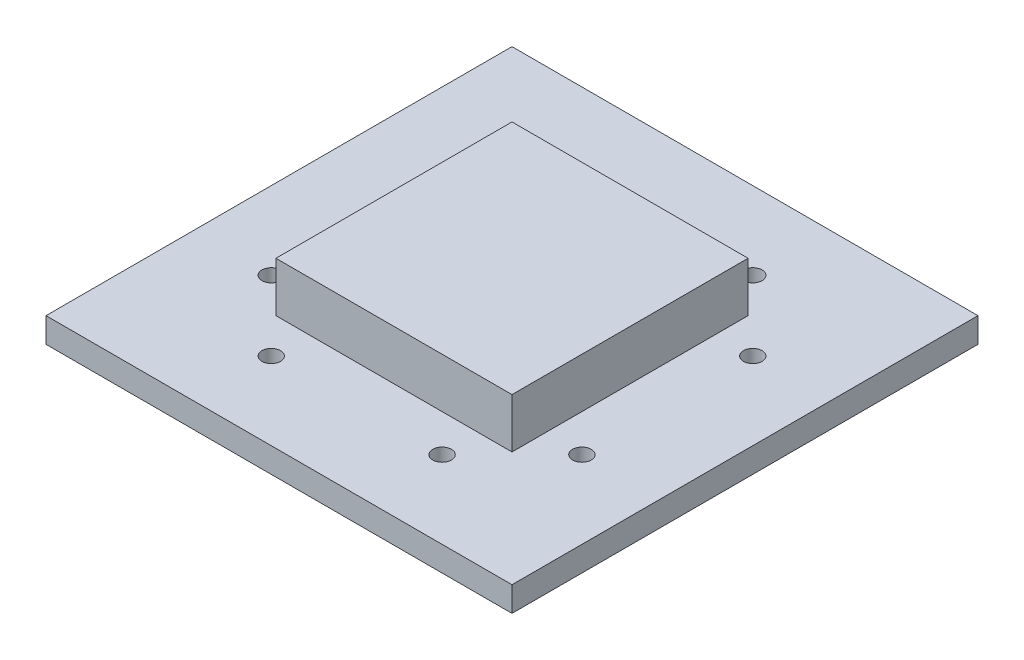
SolidWorks part; units mm, degrees
ref_plane "Front Plane" through (0, 0, 0) normal (0, 0, 1) x (1, 0, 0)
ref_plane "Top Plane" through (0, 0, 0) normal (0, 1, 0) x (1, 0, 0)
ref_plane "Right Plane" through (0, 0, 0) normal (1, 0, 0) x (0, 0, -1)
sketch "Sketch1" plane through (0, 0, 0) normal (0, 1, 0) x (1, 0, 0)
  line L0 (15, 0) -> (15, 30) construction
  line L1 (0, 0) -> (30, 0)
  line L2 (0, 0) -> (0, 30)
  line L3 (0, 30) -> (30, 30)
  line L4 (30, 0) -> (30, 30)
  line L5 (15, 13) -> (19.25, 13)
  dimension "D1" = 30
  dimension "D2" = 30
  dimension "D3" = 4.25
  dimension "D4" = 13
extrude "Boss-Extrude1" add sketch "Sketch1" along normal blind 1.6
sketch "Sketch2" plane through (0, 1.6, 0) normal (0, 1, 0) x (1, 0, 0)
  line L0 (15, 30) -> (15, 0) construction
  line L1 (0, 30) -> (30, 30) construction
  line L2 (0, 0) -> (30, 0) construction
  line L3 (15, 5) -> (20.5, 5) construction
  line L4 (30, 15) -> (0, 15) construction
  line L5 (30, 0) -> (30, 30) construction
  line L6 (0, 0) -> (0, 30) construction
  circle A0 centre (20.5, 5) radius 0.6
  circle A1 centre (9.5, 5) radius 0.6
  circle A2 centre (20.5, 25) radius 0.6
  circle A3 centre (9.5, 25) radius 0.6
  dimension "D3" = 1.2
  dimension "D1" = 5.5
  dimension "D2" = 10
extrude "Cut-Extrude1" cut sketch "Sketch2" against normal blind 1.6
pattern_circular "CirPattern1" count 2 every 90 about axis through (15, 0, -15) along (0, 1, 0) of "Cut-Extrude1"
sketch "Sketch4" plane through (0, 1.6, 0) normal (0, 1, 0) x (1, 0, 0)
  line L0 (0, 15) -> (30, 15) construction
  line L1 (0, 0) -> (0, 30) construction
  line L2 (30, 0) -> (30, 30) construction
  line L3 (15, 0) -> (15, 15) construction
  line L4 (0, 0) -> (30, 0) construction
  line L6 (7.4, 22.6) -> (22.6, 22.6)
  line L7 (7.4, 22.6) -> (7.4, 7.4)
  line L8 (7.4, 7.4) -> (22.6, 7.4)
  line L9 (22.6, 22.6) -> (22.6, 7.4)
  line L10 (7.4, 22.6) -> (22.6, 7.4) construction
  line L11 (7.4, 7.4) -> (22.6, 22.6) construction
  dimension "D1" = 15.2
  dimension "D2" = 15.2
extrude "Boss-Extrude2" add sketch "Sketch4" along normal blind 3.2
